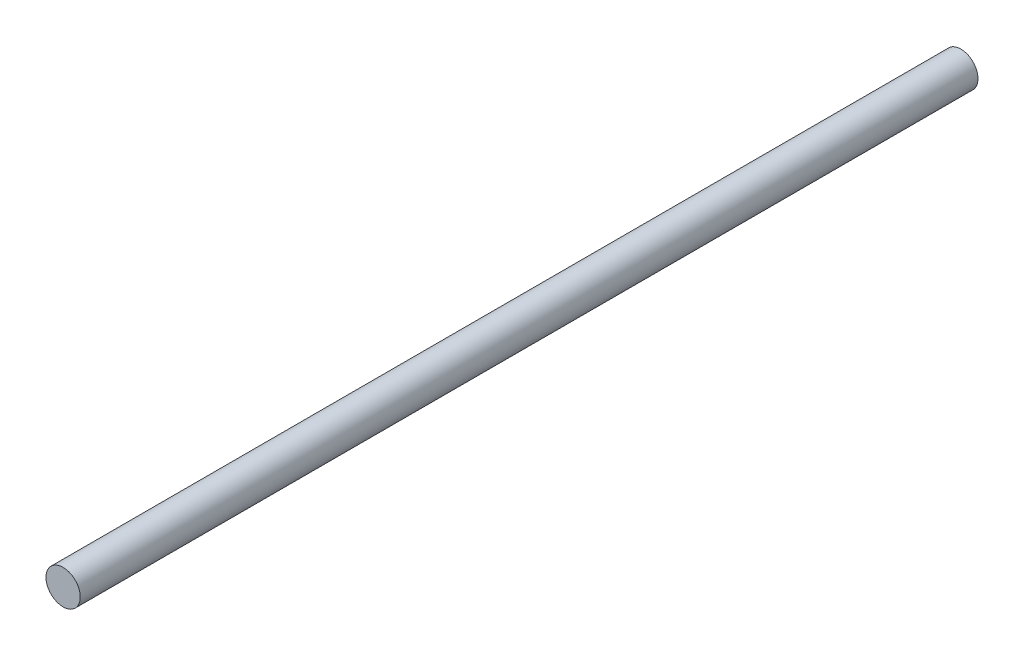
SolidWorks part; units mm, degrees
ref_plane "Front Plane" through (0, 0, 0) normal (0, 0, 1) x (1, 0, 0)
ref_plane "Top Plane" through (0, 0, 0) normal (0, 1, 0) x (1, 0, 0)
ref_plane "Right Plane" through (0, 0, 0) normal (1, 0, 0) x (0, 0, -1)
sketch "Sketch1" plane through (0, 0, 0) normal (0, 0, 1) x (1, 0, 0)
  circle A0 centre (0, 0) radius 0.5
  dimension "D1" = 1
extrude "Boss-Extrude1" add sketch "Sketch1" along normal blind 26.2
